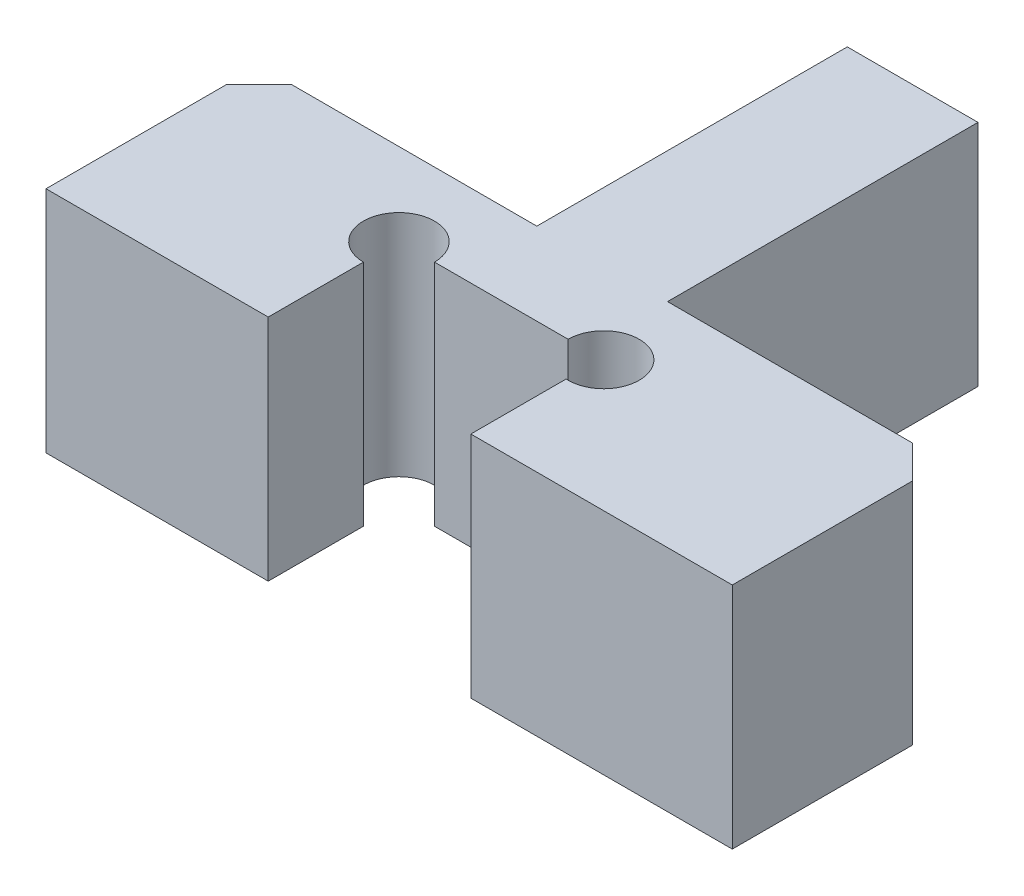
SolidWorks part; units mm, degrees
ref_plane "Front Plane" through (0, 0, 0) normal (0, 0, 1) x (1, 0, 0)
ref_plane "Top Plane" through (0, 0, 0) normal (0, 1, 0) x (1, 0, 0)
ref_plane "Right Plane" through (0, 0, 0) normal (1, 0, 0) x (0, 0, -1)
sketch "Sketch1" plane through (0, 0, 0) normal (0, 1, 0) x (1, 0, 0)
  line L0 (-5.25, -0.5142) -> (-1.85, -0.5142)
  line L1 (5.25, -0.5142) -> (5.25, 2.745)
  line L2 (5.25, 2.745) -> (1, 2.745)
  line L3 (1, 2.745) -> (1, 7.495)
  line L4 (1, 7.495) -> (-1, 7.495)
  line L5 (-1, 7.495) -> (-1, 2.745)
  line L6 (-1, 2.745) -> (-5.25, 2.745)
  line L7 (-5.25, 2.745) -> (-5.25, -0.5142)
  line L8 (1.25, -0.5142) -> (5.25, -0.5142)
  line L9 (-1.85, -0.5142) -> (1.25, -0.5142) construction
  line L10 (-1.85, -0.5142) -> (-1.85, 0.942)
  line L11 (-1.3062, 1.4858) -> (0.7384, 1.4858)
  line L12 (1.25, -0.5142) -> (1.25, 0.943)
  line L13 (-1.85, -0.5142) -> (1.25, -0.5142) construction
  line L14 (1, -1.6642) -> (1, 1.2358) construction
  line L15 (-1, 1.2358) -> (1, 1.2358) construction
  line L16 (10.5409, 5.745) -> (-27.3169, 5.745) construction
  line L17 (12.612, 2.745) -> (-26.388, 2.745) construction
  arc A0 (-1.3062, 1.4858) -> (-1.85, 0.942) centre (-1.85, 1.4858) ccw
  arc A1 (1.25, 0.943) -> (0.7384, 1.4858) centre (1.2822, 1.4858) ccw
  point P4 (0, 0)
  point P24 (0, 0)
  point P25 (0, 7.495)
  point P29 (0, 0)
  point P30 (0, 0)
  dimension "D1" = 0.25
  dimension "D2" = 0.25
  dimension "D3" = 1.75
  dimension "D4" = 2
  dimension "D5" = 0.5
  dimension "D6" = 4.25
extrude "Boss-Extrude1" add sketch "Sketch1" along normal blind 3.5 contours L6 L7 L0 L10 A0 L11 A1 L12 L8 L1 L2 L3 L4 L5
chamfer "Chamfer1" distance 0.5 angle 45 2 edges at (-5.25, 1.75, -2.745) (5.25, 1.75, -2.745)
